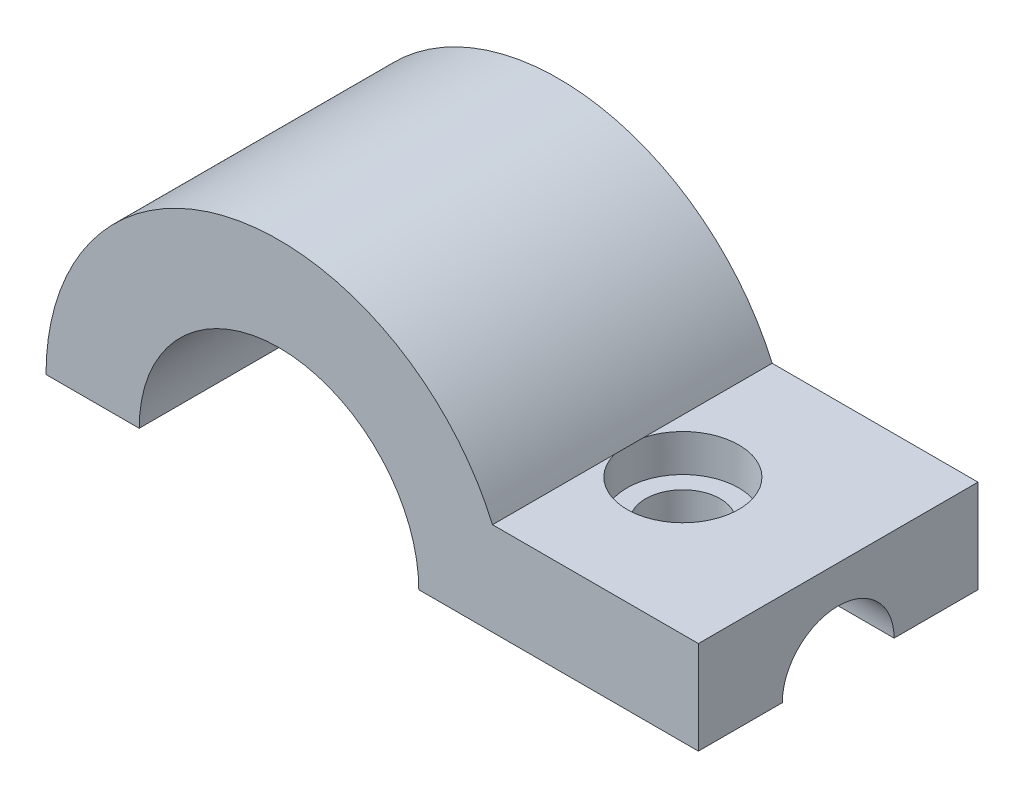
SolidWorks part; units mm, degrees
ref_plane "前视基准面" through (0, 0, 0) normal (0, 0, 1) x (1, 0, 0)
ref_plane "上视基准面" through (0, 0, 0) normal (0, 1, 0) x (1, 0, 0)
ref_plane "右视基准面" through (0, 0, 0) normal (1, 0, 0) x (0, 0, -1)
sketch "草图2" plane through (0, 0, 0) normal (0, 0, 1) x (1, 0, 0)
  line L0 (-11.25, 0) -> (-10.75, 0)
  line L1 (-7.75, 0) -> (-7.75, 0.5)
  line L2 (-7.75, 0.5) -> (-8.8544, 0.5)
  line L3 (-9.25, 0) -> (-7.75, 0)
  arc A0 (-9.25, 0) -> (-10.75, 0) centre (-10, 0) ccw
  arc A1 (-8.8544, 0.5) -> (-11.25, 0) centre (-10, 0) ccw
  dimension "D1" = 2.5
  dimension "D2" = 0.5
  dimension "D3" = 1.5
extrude "凸台-拉伸1" add sketch "草图2" against normal blind 1.5
sketch "草图3" plane through (0, 0.5, 0) normal (0, 1, 0) x (1, 0, 0)
  circle A0 centre (-8.5648, 0.7315) radius 0.2
extrude "切除-拉伸1" cut sketch "草图3" against normal blind 1.5
sketch "草图4" plane through (-7.75, 0, 0) normal (1, 0, 0) x (0, 0, -1)
  line L0 (1.5, 0) -> (0, 0) construction
  circle A0 centre (0.75, 0) radius 0.3
extrude "切除-拉伸2" cut sketch "草图4" against normal blind 0.5
sketch "草图5" plane through (0, 0.5, 0) normal (0, 1, 0) x (1, 0, 0)
  circle A0 centre (-8.5648, 0.7315) radius 0.3
extrude "切除-拉伸3" cut sketch "草图5" against normal blind 0.2
